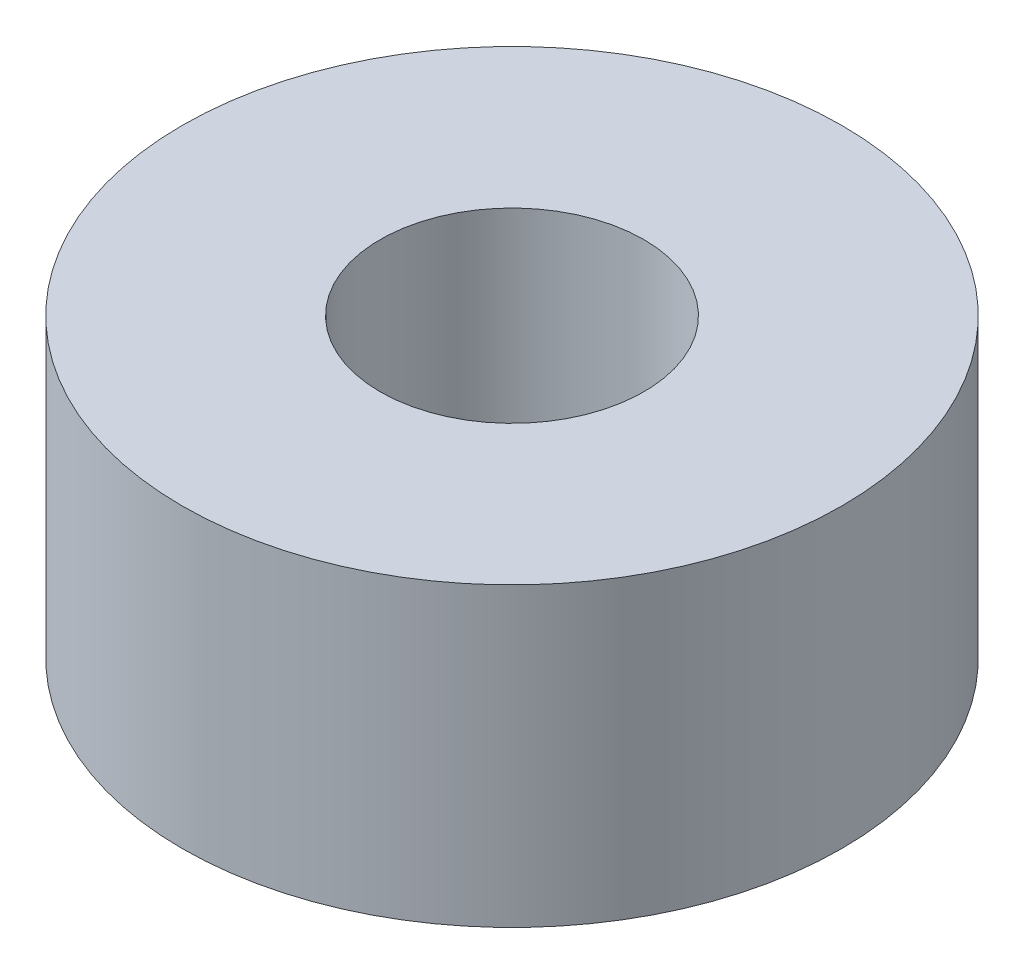
SolidWorks part; units mm, degrees
ref_plane "前视基准面" through (0, 0, 0) normal (0, 0, 1) x (1, 0, 0)
ref_plane "上视基准面" through (0, 0, 0) normal (0, 1, 0) x (1, 0, 0)
ref_plane "右视基准面" through (0, 0, 0) normal (1, 0, 0) x (0, 0, -1)
sketch "草图1" plane through (0, 0, 0) normal (0, 1, 0) x (1, 0, 0)
  circle A0 centre (0, 0) radius 2
  circle A1 centre (0, 0) radius 5
extrude "凸台-拉伸1" add sketch "草图1" along normal blind 4.5
